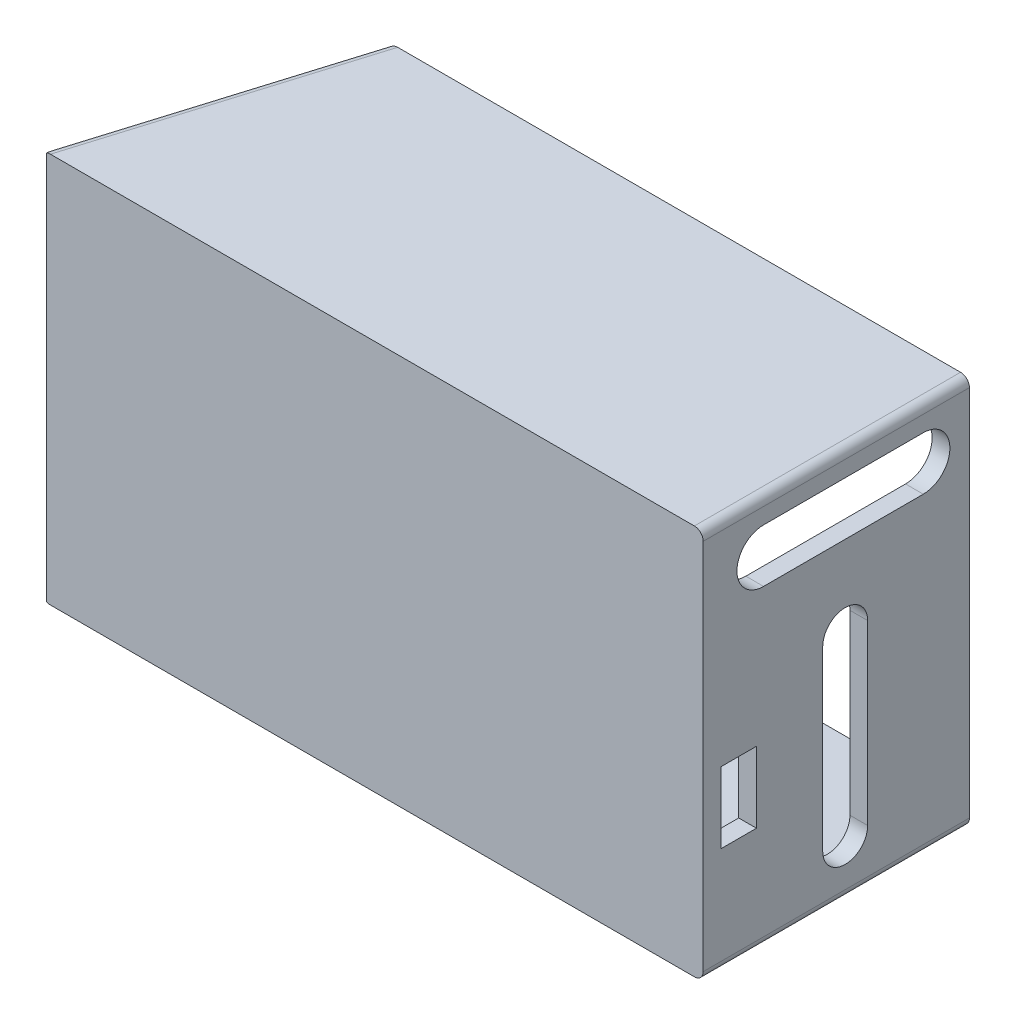
SolidWorks part; units mm, degrees
ref_plane "Plan de face" through (0, 0, 0) normal (0, 0, 1) x (1, 0, 0)
ref_plane "Plan de dessus" through (0, 0, 0) normal (0, 1, 0) x (1, 0, 0)
ref_plane "Plan de droite" through (0, 0, 0) normal (1, 0, 0) x (0, 0, -1)
sketch "Esquisse1" plane through (0, 0, 0) normal (0, 0, 1) x (1, 0, 0)
  line L1 (-114.9307, 45.7412) -> (70.0693, 45.7412)
  line L2 (-114.9307, 45.7412) -> (-114.9307, -64.2588)
  line L3 (-114.9307, -64.2588) -> (70.0693, -64.2588)
  line L4 (70.0693, 45.7412) -> (70.0693, -64.2588)
  dimension "D1" = 110
  dimension "D2" = 185
extrude "Boss.-Extru.1" add sketch "Esquisse1" along normal blind 5
sketch "Esquisse3" plane through (0, 45.7412, 0) normal (0, 1, 0) x (1, 0, 0)
  line L0 (-114.9307, 0) -> (-93.6163, 70)
  line L1 (-93.6163, 70) -> (-88.6163, 70)
  line L2 (-88.6163, 70) -> (-109.9307, 0)
  line L3 (70.0693, 0) -> (-114.9307, 0) construction
  line L4 (-109.9307, 0) -> (-114.9307, 0)
  dimension "D1" = 70
  dimension "D2" = 5
extrude "Boss.-Extru.2" add sketch "Esquisse3" against normal blind 110
sketch "Esquisse4" plane through (0, 45.7412, 0) normal (0, 1, 0) x (1, 0, 0)
  line L0 (-109.9307, 0) -> (-88.6163, 70)
  line L1 (-109.9307, 0) -> (70.0693, 0)
  line L2 (70.0693, 0) -> (70.0693, 70)
  line L3 (70.0693, 70) -> (-88.6163, 70)
extrude "Boss.-Extru.3" add sketch "Esquisse4" against normal blind 5
sketch "Esquisse7" plane through (0, -64.2588, 0) normal (0, -1, 0) x (1, 0, 0)
  line L0 (-109.9307, 0) -> (-88.6163, -70)
  line L1 (-88.6163, -70) -> (70.0693, -70)
  line L2 (70.0693, -70) -> (70.0693, 0)
  line L3 (70.0693, 0) -> (-109.9307, 0)
extrude "Boss.-Extru.4" add sketch "Esquisse7" against normal blind 5
sketch "Esquisse8" plane through (70.0693, 0, 0) normal (1, 0, 0) x (0, 0, -1)
  line L0 (70, 40.7412) -> (0, 40.7412)
  line L1 (0, 40.7412) -> (0, -59.2588)
  line L2 (0, -59.2588) -> (70, -59.2588)
  line L3 (70, -59.2588) -> (70, 40.7412)
  line L4 (35, 0.7412) -> (35, -49.2588) construction
  line L5 (41.3317, 0.7412) -> (41.3317, -49.2588)
  line L6 (28.6683, 0.7412) -> (28.6683, -49.2588)
  line L7 (12, 31.2412) -> (57, 31.2412) construction
  line L8 (12, 38.7412) -> (57, 38.7412)
  line L9 (12, 23.7412) -> (57, 23.7412)
  arc A0 (41.3317, 0.7412) -> (28.6683, 0.7412) centre (35, 0.7412) ccw
  arc A1 (28.6683, -49.2588) -> (41.3317, -49.2588) centre (35, -49.2588) ccw
  arc A2 (12, 38.7412) -> (12, 23.7412) centre (12, 31.2412) ccw
  arc A3 (57, 23.7412) -> (57, 38.7412) centre (57, 31.2412) ccw
  point P10 (35, -24.2588)
  point P17 (34.5, 31.2412)
  dimension "D1" = 35
  dimension "D2" = 50
  dimension "D3" = 10
  dimension "D4" = 45
  dimension "D5" = 15
  dimension "D6" = 17
  dimension "D7" = 12
sketch "Esquisse9" plane through (0, 0, 0) normal (0, 0, -1) x (-1, 0, 0)
extrude "Boss.-Extru.6" add sketch "Esquisse8" against normal blind 5
sketch "Esquisse10" plane through (-105.179, 0, -32.0261) normal (-0.9566, 0, -0.2913) x (-0.2913, 0, 0.9566)
  line L0 (0, 45.7412) -> (0, -64.2588) construction
  line L1 (-39.6953, 45.7412) -> (33.4778, 45.7412) construction
  line L2 (-39.6953, -64.2588) -> (33.4778, -64.2588) construction
  line L3 (-18, -64.2588) -> (-18, 45.7412) construction
  line L5 (-8, 45.7412) -> (-8, -64.2588) construction
  circle A0 centre (-8, 38.7412) radius 2.5
  circle A1 centre (-8, 30.7412) radius 2.5
  circle A2 centre (-8, 22.7412) radius 2.5
  circle A3 centre (-8, 14.7412) radius 2.5
  circle A4 centre (-8, 6.7412) radius 2.5
  circle A5 centre (-8, -1.2588) radius 2.5
  circle A6 centre (-8, -9.2588) radius 2.5
  circle A7 centre (-8, -17.2588) radius 2.5
  circle A8 centre (-8, -25.2588) radius 2.5
  circle A9 centre (-8, -33.2588) radius 2.5
  circle A10 centre (-8, -41.2588) radius 2.5
  circle A11 centre (-8, -49.2588) radius 2.5
  circle A12 centre (-8, -57.2588) radius 2.5
  circle A13 centre (-28, -57.2588) radius 2.5
  circle A14 centre (-28, -49.2588) radius 2.5
  circle A15 centre (-28, -41.2588) radius 2.5
  circle A16 centre (-28, -9.2588) radius 2.5
  circle A17 centre (-28, -17.2588) radius 2.5
  circle A18 centre (-28, -25.2588) radius 2.5
  circle A19 centre (-28, -33.2588) radius 2.5
  circle A20 centre (-28, -1.2588) radius 2.5
  circle A21 centre (-28, 6.7412) radius 2.5
  circle A22 centre (-28, 14.7412) radius 2.5
  circle A23 centre (-28, 22.7412) radius 2.5
  circle A24 centre (-28, 30.7412) radius 2.5
  circle A25 centre (-28, 38.7412) radius 2.5
  dimension "D3" = 5
  dimension "D1" = 18
  dimension "D2" = 10
  dimension "D4" = 7
  dimension "D5" = 13
extrude "Enlèv. mat.-Extru.1" cut sketch "Esquisse10" against normal blind 5
sketch "Esquisse13" plane through (0, 0, -70) normal (0, 0, -1) x (-1, 0, 0)
  line L0 (-65.0693, 40.7412) -> (88.6163, 40.7412) construction
  line L1 (88.6163, -59.2588) -> (88.6163, 40.7412) construction
  line L2 (88.6163, -59.2588) -> (-65.0693, -59.2588) construction
  line L3 (-65.0693, -59.2588) -> (-65.0693, 40.7412) construction
  circle A0 centre (-67.0693, 42.7412) radius 1
  circle A1 centre (-67.0693, -61.2588) radius 1
  circle A2 centre (90.6163, -61.2588) radius 1
  circle A3 centre (90.6163, 42.7412) radius 1
  dimension "D1" = 2
  dimension "D2" = 2
  dimension "D3" = 2
  dimension "D4" = 2
  dimension "D5" = 2
  dimension "D6" = 2
  dimension "D7" = 2
  dimension "D8" = 2
  dimension "D9" = 2
  dimension "D10" = 2
  dimension "D11" = 2
  dimension "D12" = 2
extrude "Enlèv. mat.-Extru.2" cut sketch "Esquisse13" against normal blind 10
sketch "Esquisse14" plane through (0, -64.2588, 0) normal (0, -1, 0) x (-1, 0, 0)
  line L0 (-70.0693, 70) -> (93.6163, 70) construction
  line L1 (-70.0693, -5) -> (-70.0693, 70) construction
  circle A0 centre (-60.0693, 60) radius 2.5
  dimension "D1" = 5
  dimension "D2" = 10
  dimension "D3" = 10
sketch "Esquisse15" plane through (70.0693, 0, 0) normal (1, 0, 0) x (0, 0, -1)
  line L0 (-5, -64.2588) -> (-5, 45.7412) construction
  line L1 (0, -14.2588) -> (10, -14.2588)
  line L2 (0, -14.2588) -> (0, -34.2588)
  line L3 (0, -34.2588) -> (10, -34.2588)
  line L4 (10, -14.2588) -> (10, -34.2588)
  line L5 (-5, -64.2588) -> (70, -64.2588) construction
  dimension "D1" = 10
  dimension "D2" = 20
  dimension "D3" = 5
  dimension "D4" = 30
extrude "Enlèv. mat.-Extru.3" cut sketch "Esquisse15" against normal blind 10
extrude "Enlèv. mat.-Extru.4" cut sketch "Esquisse14" against normal blind 10
fillet "Congé2" radius 2.5 1 edges at (-104.2735, -64.2588, -35)
fillet "Congé3" radius 2.5 1 edges at (-104.2735, 45.7412, -35)
fillet "Congé4" radius 2.5 1 edges at (70.0693, -64.2588, -32.5)
fillet "Congé5" radius 2.5 1 edges at (70.0693, 45.7412, -32.5)
